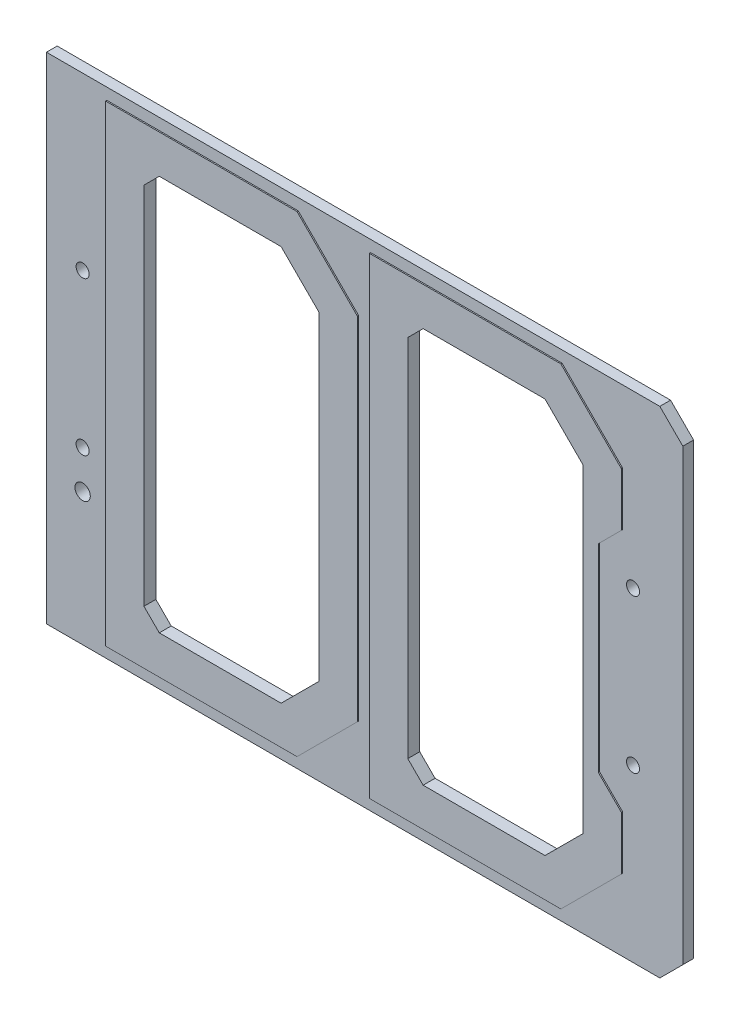
SolidWorks part; units mm, degrees
ref_plane "Front Plane" through (0, 0, 0) normal (0, 0, 1) x (1, 0, 0)
ref_plane "Top Plane" through (0, 0, 0) normal (0, 1, 0) x (1, 0, 0)
ref_plane "Right Plane" through (0, 0, 0) normal (1, 0, 0) x (0, 0, -1)
sketch "Sketch1" plane through (0, 0, 0) normal (0, 0, 1) x (1, 0, 0)
  line L0 (-46.7106, 41) -> (-46.7106, -41) construction
  line L1 (-52.705, -41) -> (52.705, -41)
  line L2 (-52.705, -41) -> (-52.705, 41)
  line L3 (-52.705, 41) -> (52.705, 41)
  line L4 (52.705, -41) -> (52.705, 41)
  line L5 (-52.705, -41) -> (52.705, 41) construction
  line L6 (-52.705, 41) -> (52.705, -41) construction
  line L7 (44.45, 41) -> (44.45, -41) construction
  circle A3 centre (44.45, 12.7) radius 1.0795
  circle A4 centre (44.45, -12.7) radius 1.0795
  circle A5 centre (-46.7106, 12.7) radius 1.0795
  circle A6 centre (-46.7106, -12.7) radius 1.0795
  circle A10 centre (-46.7106, -19.05) radius 1.27
  point P0 (0, 0)
  dimension "D15" = 2.54
  dimension "D3" = 2.159
  dimension "D1" = 82
  dimension "D2" = 105.41
  dimension "D7" = 5.9944
  dimension "D11" = 8.255
  dimension "D4" = 28.3
  dimension "D5" = 6.35
  dimension "D9" = 28.3
extrude "Boss-Extrude1" add sketch "Sketch1" along normal blind 1.778
sketch "Sketch2" plane through (0, 0, 1.778) normal (0, 0, 1) x (1, 0, 0)
  line L0 (-11, 39.095) -> (-1, 29.095)
  line L1 (-42.705, 39.095) -> (-11, 39.095)
  line L2 (-42.705, 39.095) -> (-42.705, -39.095)
  line L3 (-42.705, -39.095) -> (-11, -39.095)
  line L4 (-1, 29.095) -> (-1, -29.095)
  line L5 (-42.705, 39.095) -> (-1, -39.095) construction
  line L6 (-42.705, -39.095) -> (-1, 39.095) construction
  line L11 (42.705, 20.205) -> (38.895, 16.395)
  line L12 (38.895, 16.395) -> (38.895, -16.395)
  line L17 (38.895, -16.395) -> (42.705, -20.205)
  line L18 (-52.705, 41) -> (52.705, 41) construction
  line L23 (-52.705, -41) -> (52.705, -41) construction
  line L24 (42.705, -20.205) -> (42.705, -29.095)
  line L43 (1, 39.095) -> (32.705, 39.095)
  line L44 (1, 39.095) -> (1, -39.095)
  line L45 (1, -39.095) -> (32.705, -39.095)
  line L46 (42.705, 29.095) -> (42.705, 20.205)
  line L47 (1, 39.095) -> (42.705, -39.095) construction
  line L48 (1, -39.095) -> (42.705, 39.095) construction
  line L49 (-1, -29.095) -> (-11, -39.095)
  line L62 (32.705, -39.095) -> (42.705, -29.095)
  line L63 (32.705, 39.095) -> (42.705, 29.095)
  line L64 (-52.705, -41) -> (-52.705, 41) construction
  line L65 (52.705, -41) -> (52.705, 41) construction
  point P4 (-21.8525, 0)
  point P39 (21.8525, 0)
  point P76 (52.705, 0)
  dimension "D25" = 10
  dimension "D26" = 10
  dimension "D3" = 2
  dimension "D6" = 3.81
  dimension "D7" = 45
  dimension "D8" = 45
  dimension "D9" = 8.89
  dimension "D10" = 8.89
  dimension "D11" = 1.905
  dimension "D12" = 1.905
extrude "Boss-Extrude2" add sketch "Sketch2" along normal blind 0.2
sketch "Sketch3" plane through (0, 0, 1.978) normal (0, 0, 1) x (1, 0, 0)
  line L0 (-36.355, -32.745) -> (-36.355, 32.745)
  line L1 (-36.355, 32.745) -> (-13.6303, 32.745)
  line L2 (-13.6303, 32.745) -> (-7.35, 26.4647)
  line L3 (-7.35, 26.4647) -> (-7.35, -26.4647)
  line L4 (-7.35, -26.4647) -> (-13.6303, -32.745)
  line L5 (-13.6303, -32.745) -> (-36.355, -32.745)
  line L6 (7.35, -32.745) -> (7.35, 32.745)
  line L7 (7.35, 32.745) -> (30.0747, 32.745)
  line L8 (30.0747, 32.745) -> (36.355, 26.4647)
  line L9 (36.355, 26.4647) -> (36.355, -26.4647)
  line L10 (36.355, -26.4647) -> (30.0747, -32.745)
  line L11 (30.0747, -32.745) -> (7.35, -32.745)
  line L12 (-11, -39.095) -> (-1, -29.095) construction
  line L13 (-1, 29.095) -> (-11, 39.095) construction
  line L14 (-42.705, 39.095) -> (-42.705, -39.095) construction
  line L15 (-1, -29.095) -> (-1, 29.095) construction
  line L16 (-11, 39.095) -> (-42.705, 39.095) construction
  line L17 (-1, 29.095) -> (-11, 39.095) construction
  line L18 (-42.705, -39.095) -> (-11, -39.095) construction
  line L19 (1, 39.095) -> (1, -39.095) construction
  dimension "D5" = 6.35
  dimension "D1" = 6.35
  dimension "D2" = 6.35
  dimension "D3" = 6.35
  dimension "D4" = 6.35
  dimension "D6" = 6.35
extrude "Cut-Extrude1" cut sketch "Sketch3" against normal through all
chamfer "Chamfer1" distance 2.54 angle 45 4 edges at (7.35, -32.745, 0.989) (-36.355, -32.745, 0.989) (7.35, 32.745, 0.989) (-36.355, 32.745, 0.989)
chamfer "Chamfer2" distance 3.81 angle 45 2 edges at (52.705, -41, 0.889) (52.705, 41, 0.889)
equation "\"D26@Sketch2\"=\"D25@Sketch2\""
equation "\"D8@Sketch1\"=\"D6@Sketch1\""
equation "\"D4@Sketch1\"=(\"D1@Sketch1\"-\"D6@Sketch1\")/2"
equation "\"D9@Sketch1\"=\"D4@Sketch1\""
equation "\"D2@Sketch3\"=\"D1@Sketch3\""
equation "\"D3@Sketch3\"=\"D1@Sketch3\""
equation "\"D4@Sketch3\"=\"D3@Sketch3\""
equation "\"D5@Sketch3\"=\"D1@Sketch3\""
equation "\"D6@Sketch3\"=\"D1@Sketch3\""
equation "\"D7@Sketch1\"=.754/2-.141"
equation "\"D10@Sketch2\"=\"D9@Sketch2\""
